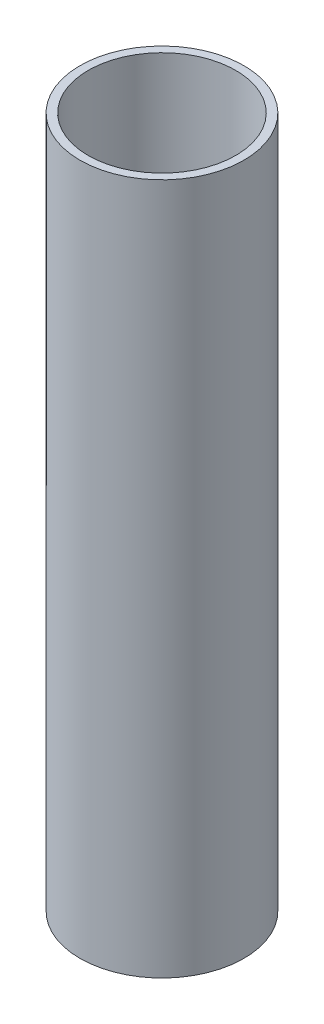
SolidWorks part; units mm, degrees
ref_plane "Front Plane" through (0, 0, 0) normal (0, 0, 1) x (1, 0, 0)
ref_plane "Top Plane" through (0, 0, 0) normal (0, 1, 0) x (1, 0, 0)
ref_plane "Right Plane" through (0, 0, 0) normal (1, 0, 0) x (0, 0, -1)
sketch "Sketch1" plane through (0, 0, 0) normal (0, 1, 0) x (1, 0, 0)
  circle A0 centre (0, 0) radius 30
  dimension "D1" = 60
extrude "Boss-Extrude1" add sketch "Sketch1" along normal blind 3
sketch "Sketch2" plane through (0, 3, 0) normal (0, 1, 0) x (1, 0, 0)
  circle A0 centre (0, 0) radius 30
  circle A1 centre (0, 0) radius 27
  dimension "D1" = 3
extrude "Boss-Extrude2" add sketch "Sketch2" along normal blind 250
sketch "Sketch3" plane through (0, 0, 0) normal (0, -1, 0) x (1, 0, 0)
  line L0 (0, 0) -> (0, 12.25) construction
  line L1 (0, 0) -> (0, -12.25) construction
  line L2 (-1.5, 0) -> (-1.5, 12.25)
  line L3 (-1.5, 0) -> (-1.5, -12.25)
  line L4 (1.5, 0) -> (1.5, 12.25)
  line L5 (1.5, 0) -> (1.5, -12.25)
  line L6 (-1.5, 12.25) -> (1.5, 12.25)
  line L7 (-1.5, -12.25) -> (1.5, -12.25)
  dimension "D1" = 12.25
  dimension "D2" = 12.25
  dimension "D3" = 1.5
  dimension "D4" = 1.5
extrude "Cut-Extrude1" cut sketch "Sketch3" against normal blind 44
